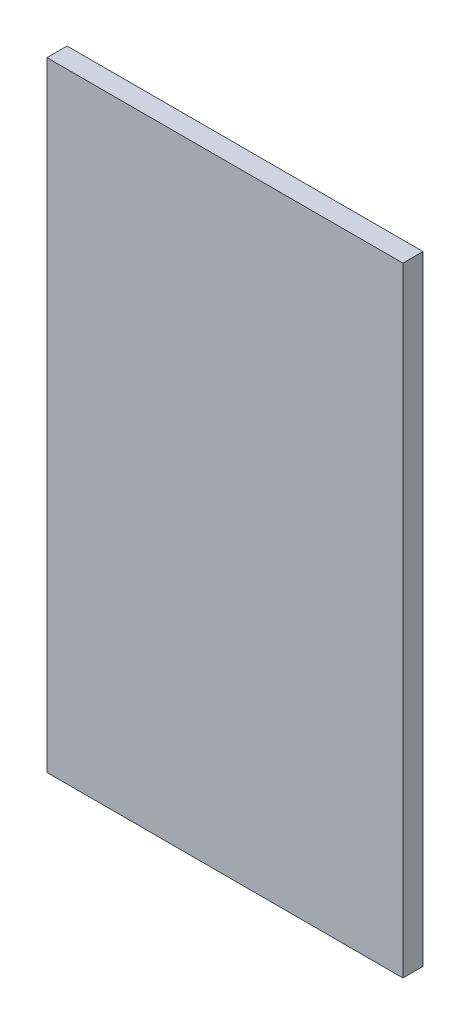
SolidWorks part; units mm, degrees
ref_plane "Front Plane" through (0, 0, 0) normal (0, 0, 1) x (1, 0, 0)
ref_plane "Top Plane" through (0, 0, 0) normal (0, 1, 0) x (1, 0, 0)
ref_plane "Right Plane" through (0, 0, 0) normal (1, 0, 0) x (0, 0, -1)
sketch "Sketch1" plane through (0, 0, 0) normal (0, 0, 1) x (1, 0, 0)
  line L1 (115, 200) -> (-115, 200)
  line L2 (115, 200) -> (115, -200)
  line L3 (115, -200) -> (-115, -200)
  line L4 (-115, 200) -> (-115, -200)
  line L5 (115, 200) -> (-115, -200) construction
  line L6 (115, -200) -> (-115, 200) construction
  point P0 (0, 0)
  dimension "D1" = 230
  dimension "D2" = 400
extrude "Boss-Extrude1" add sketch "Sketch1" along normal blind 13
fillet "Fillet1" [suppressed] radius 5
sketch "Sketch2" plane through (0, 0, 13) normal (0, 0, 1) x (1, 0, 0)
  line L1 (-23, 188.85) -> (23, 188.85) construction
  line L2 (-23, 188.85) -> (-23, 175.85) construction
  line L3 (-23, 175.85) -> (23, 175.85) construction
  line L4 (23, 188.85) -> (23, 175.85) construction
  circle A0 centre (-23, 188.85) radius 2.1
  circle A1 centre (23, 188.85) radius 2.1
  circle A2 centre (23, 175.85) radius 2.1
  circle A3 centre (-23, 175.85) radius 2.1
  dimension "D1" = 4.2
extrude "Cut-Extrude1" [suppressed] cut sketch "Sketch2" against normal through all
sketch "Sketch3" plane through (0, 0, 0) normal (0, 0, -1) x (-1, 0, 0)
  line L0 (0, 0) -> (0, 299.0074) construction
  line L1 (-40, 171.9865) -> (-40, 146.9865) construction
  line L2 (-40, 146.9865) -> (-40, 121.9865) construction
  line L3 (-40, 121.9865) -> (0, 121.9865) construction
  circle A0 centre (-40, 121.9865) radius 2.75
  circle A1 centre (-40, 146.9865) radius 2.75
  circle A2 centre (-40, 171.9865) radius 2.75
  circle A3 centre (40, 121.9865) radius 2.75
  circle A4 centre (40, 146.9865) radius 2.75
  circle A5 centre (40, 171.9865) radius 2.75
  dimension "D1" = 5.5
extrude "Cut-Extrude2" [suppressed] cut sketch "Sketch3" against normal through all
sketch "Sketch4" plane through (0, 0, 13) normal (0, 0, 1) x (1, 0, 0)
  line L0 (0, 200) -> (0, -200) construction
  line L1 (115, 200) -> (-115, 200) construction
  line L2 (-115, -200) -> (115, -200) construction
  line L3 (102.75, -61.6667) -> (102.75, -123.3333) construction
  line L4 (102.75, -123.3333) -> (102.75, -185) construction
  line L5 (102.75, -185) -> (57.25, -185) construction
  line L6 (57.25, -185) -> (-57.25, -185) construction
  line L7 (-57.25, -185) -> (-102.75, -185) construction
  line L8 (-102.75, -123.3333) -> (-57.25, -123.3333) construction
  line L9 (-57.25, -123.3333) -> (57.25, -123.3333) construction
  line L10 (57.25, -123.3333) -> (102.75, -123.3333) construction
  circle A0 centre (-102.75, 185) radius 2.1
  circle A1 centre (-102.75, 123.3333) radius 2.1
  circle A2 centre (-102.75, 61.6667) radius 2.1
  circle A3 centre (-102.75, 0) radius 2.1
  circle A4 centre (-102.75, -61.6667) radius 2.1
  circle A5 centre (-102.75, -123.3333) radius 3.3
  circle A6 centre (-102.75, -185) radius 3.3
  circle A7 centre (-57.25, 185) radius 2.1
  circle A8 centre (-57.25, 123.3333) radius 2.1
  circle A9 centre (-57.25, 61.6667) radius 2.1
  circle A10 centre (-57.25, 0) radius 2.1
  circle A11 centre (-57.25, -61.6667) radius 2.1
  circle A12 centre (-57.25, -123.3333) radius 2.1
  circle A13 centre (-57.25, -185) radius 2.1
  circle A14 centre (57.25, -185) radius 2.1
  circle A15 centre (57.25, -123.3333) radius 2.1
  circle A16 centre (57.25, -61.6667) radius 2.1
  circle A17 centre (57.25, 0) radius 2.1
  circle A18 centre (57.25, 61.6667) radius 2.1
  circle A19 centre (57.25, 123.3333) radius 2.1
  circle A20 centre (57.25, 185) radius 2.1
  circle A21 centre (102.75, -185) radius 3.3
  circle A22 centre (102.75, -123.3333) radius 3.3
  circle A23 centre (102.75, -61.6667) radius 2.1
  circle A24 centre (102.75, 0) radius 2.1
  circle A25 centre (102.75, 61.6667) radius 2.1
  circle A26 centre (102.75, 123.3333) radius 2.1
  circle A27 centre (102.75, 185) radius 2.1
  dimension "D1" = 4.2
  dimension "D2" = 6.6
extrude "Cut-Extrude3" [suppressed] cut sketch "Sketch4" against normal through all
sketch "Sketch6" [suppressed] plane through (0, 0, 13) normal (0, 0, 1) x (1, 0, 0)
  line L0 (-57.25, -123.3333) -> (57.25, -123.3333) construction
  line L1 (-32.5, -123.3333) -> (-32.5, -185) construction
  line L2 (32.5, -123.3333) -> (32.5, -185) construction
  line L3 (-57.25, -185) -> (57.25, -185) construction
  line L4 (0, -60.963) -> (0, -151.8475) construction
  line L5 (-32.5, -123.3333) -> (0, -123.3333) construction
  line L6 (102.75, 61.6667) -> (102.75, -61.6667) construction
  line L7 (0, -123.3333) -> (32.5, -123.3333) construction
  line L8 (32.5, -16.08) -> (102.75, -16.08) construction
  line L9 (32.5, 45.5867) -> (102.75, 45.5867) construction
  line L10 (32.5, 45.5867) -> (32.5, -123.3333) construction
  circle A11 centre (32.5, -123.3333) radius 3.3
  circle A12 centre (-32.5, -123.3333) radius 3.3
  circle A19 centre (-32.5, -185) radius 3.3
  circle A20 centre (32.5, -185) radius 3.3
  circle A25 centre (102.75, 45.5867) radius 2.5
  circle A26 centre (102.75, -16.08) radius 2.5
  circle A27 centre (-102.75, -16.08) radius 2.5
  circle A28 centre (-102.75, 45.5867) radius 2.5
  circle A29 centre (32.5, 45.5867) radius 2.5
  circle A30 centre (32.5, -16.08) radius 2.5
  circle A31 centre (-32.5, -16.08) radius 2.5
  circle A32 centre (-32.5, 45.5867) radius 2.5
  dimension "D2" = 6.6
  dimension "D5" = 5
  dimension "D1" = 65
  dimension "D4" = 168.92
  dimension "D3" = 61.6667
extrude "Cut-Extrude4" [suppressed] cut sketch "Sketch6" against normal through all
sketch "Sketch8" [suppressed] plane through (0, 0, 0) normal (0, 0, -1) x (-1, 0, 0)
  line L0 (37.5, 22) -> (32.5, 22) construction
  line L1 (-110, 200) -> (110, 200) construction
  circle A0 centre (37.5, 22) radius 4
  point P4 (32.5, 45.5867)
  point P8 (35, 22)
  dimension "D1" = 8
  dimension "D2" = 178
  dimension "D3" = 5
extrude "Cut-Extrude5" [suppressed] cut sketch "Sketch8" against normal mid plane 107
sketch "Sketch9" [suppressed] plane through (0, 0, 0) normal (0, 0, -1) x (-1, 0, 0)
  line L0 (0, 200) -> (0, 0) construction
  line L1 (-110, 200) -> (110, 200) construction
  line L2 (-40, 171.9865) -> (-40, 200) construction
  circle A0 centre (-40, 193.65) radius 2.1
  circle A1 centre (40, 193.65) radius 2.1
  dimension "D1" = 4.2
  dimension "D2" = 6.35
extrude "Cut-Extrude6" [suppressed] cut sketch "Sketch9" against normal through all
equation "\"M5_Thread\"= 4.2mm"
equation "\"M5_Pass\"= 5.5"
equation "\"M6_Thread\"= 5mm"
equation "\"M6_Pass\"= 6.6"
equation "\"M5_Head\"= 9mm"
equation "\"M6_Head\"= 10.5"
equation "\"M5_HeadDepth\"= 5.5"
equation "\"M6_HeadDepth\"= 5.9 + .5"
equation "\"D1@Sketch2\"=\"M5_Thread\""
equation "\"D1@Sketch3\"=\"M5_Pass\""
equation "\"D1@Sketch4\"=\"M5_Thread\""
equation "\"D2@Sketch4\"=\"M6_Pass\""
equation "\"D2@Sketch6\"=\"M6_Pass\""
equation "\"D5@Sketch6\"=\"M6_Thread\""
